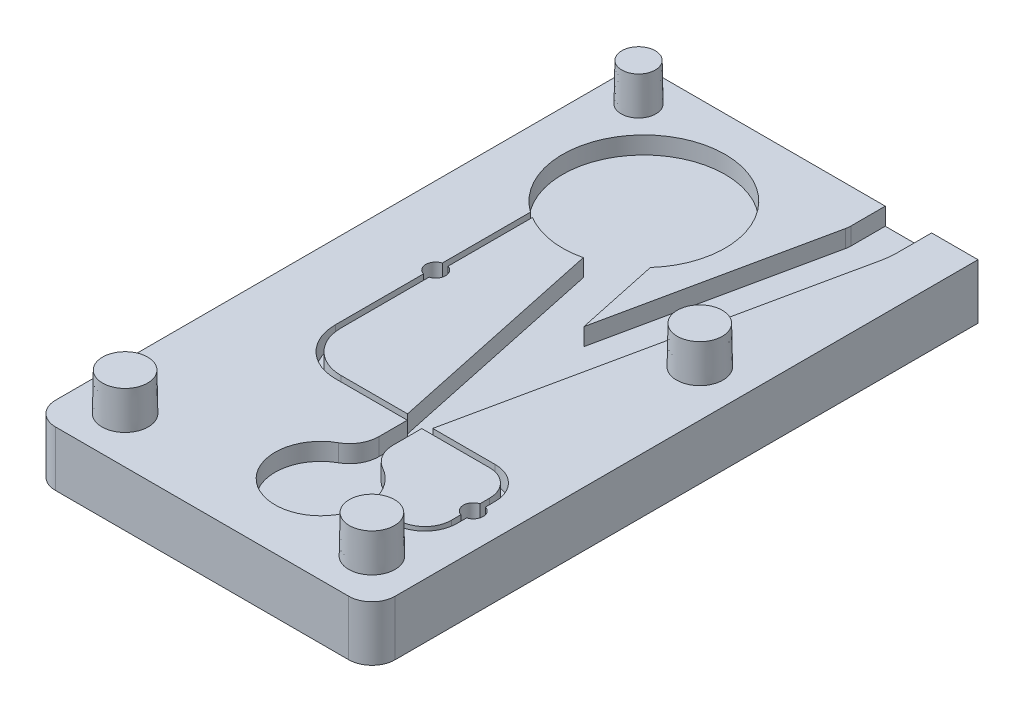
SolidWorks part; units mm, degrees
material "ABS"
ref_plane "Front Plane" through (0, 0, 0) normal (0, 0, 1) x (1, 0, 0)
ref_plane "Top Plane" through (0, 0, 0) normal (0, 1, 0) x (1, 0, 0)
ref_plane "Right Plane" through (0, 0, 0) normal (1, 0, 0) x (0, 0, -1)
sketch "Sketch1" plane through (0, 0, 0) normal (0, 1, 0) x (1, 0, 0)
  line L1 (-23.25, 41.5) -> (23.25, 41.5)
  line L2 (-23.25, 41.5) -> (-23.25, -41.5)
  line L3 (-23.25, -41.5) -> (23.25, -41.5)
  line L4 (23.25, 41.5) -> (23.25, -41.5)
  line L5 (-23.25, 41.5) -> (23.25, -41.5) construction
  line L6 (-23.25, -41.5) -> (23.25, 41.5) construction
  point P0 (0, 0)
  dimension "D1" = 46.5
  dimension "D2" = 83
extrude "Boss-Extrude1" add sketch "Sketch1" along normal blind 7.5406
sketch "Sketch2" plane through (0, 0, 0) normal (0, 1, 0) x (1, 0, 0)
  line L1 (-12.65, -10.23) -> (-12.65, 25.55) construction
  line L11 (9.4726, 31.3805) -> (10.4806, 36.123)
  line L17 (10.55, 36.7831) -> (10.55, 41.5)
  line L22 (-23.25, -41.5) -> (23.25, -41.5) construction
  line L23 (0.7075, -41.5) -> (7.6925, -41.5)
  line L24 (0.7075, -41.5) -> (0.7075, -34.6481)
  line L25 (9.4726, 31.3805) -> (4.2, 6.575)
  line L26 (15.6838, 30.0603) -> (16.6919, 34.8027)
  line L27 (4.2, 6.575) -> (0.1667, 25.55)
  line L28 (16.9, 36.7831) -> (16.9, 41.5)
  line L29 (0.1667, 25.55) -> (-6.0445, 24.2298)
  line L30 (-6.0445, 24.2298) -> (2.4737, -15.845)
  line L31 (-6.65, -16.23) -> (14.4748, -16.23) construction
  line L32 (3.2078, -16.615) -> (3.2078, -23.2943)
  line L33 (5.1922, -23.2943) -> (5.1922, -16.615)
  line L34 (4.2, 6.575) -> (4.2, 41.5) construction
  line L35 (18.4748, -20.23) -> (18.4748, -25.465) construction
  line L36 (14.4748, -29.465) -> (4.2, -29.465) construction
  line L37 (0.7075, -34.6481) -> (7.6925, -34.6481)
  line L38 (7.6925, -41.5) -> (7.6925, -34.6481)
  line L39 (15.6838, 30.0603) -> (5.9263, -15.845)
  line L40 (23.25, 41.5) -> (-23.25, 41.5) construction
  line L41 (4.2, 6.575) -> (10.6919, 6.575) construction
  line L42 (23.25, -41.5) -> (23.25, 41.5) construction
  line L43 (-23.25, 41.5) -> (-23.25, -41.5) construction
  line L44 (14.4748, -29.85) -> (4.2, -29.85)
  line L45 (18.8598, -20.23) -> (18.8598, -25.465)
  line L46 (-6.65, -15.845) -> (14.4748, -15.845)
  line L47 (-12.265, -10.23) -> (-12.265, 25.55)
  line L48 (14.4748, -29.08) -> (4.2, -29.08)
  line L49 (18.0898, -20.23) -> (18.0898, -25.465)
  line L50 (-6.65, -16.615) -> (14.4748, -16.615)
  line L51 (-13.035, -10.23) -> (-13.035, 25.55)
  line L52 (9.4726, 31.3805) -> (15.6838, 30.0603) construction
  line L53 (3.2078, -19.9546) -> (5.1922, -19.9546) construction
  line L54 (4.2, -19.9546) -> (4.2, -29.465) construction
  line L55 (10.55, 41.5) -> (16.9, 41.5)
  circle A6 centre (-6.56, 25.55) radius 11.13
  arc A7 (14.4748, -16.23) -> (18.4748, -20.23) centre (14.4748, -20.23) cw construction
  arc A8 (18.4748, -25.465) -> (14.4748, -29.465) centre (14.4748, -25.465) cw construction
  circle A9 centre (4.2, -29.465) radius 6.25
  arc A11 (-12.65, -10.23) -> (-6.65, -16.23) centre (-6.65, -10.23) ccw construction
  arc A12 (18.8598, -25.465) -> (14.4748, -29.85) centre (14.4748, -25.465) cw
  arc A13 (14.4748, -15.845) -> (18.8598, -20.23) centre (14.4748, -20.23) cw
  arc A14 (-12.265, -10.23) -> (-6.65, -15.845) centre (-6.65, -10.23) ccw
  arc A15 (18.0898, -25.465) -> (14.4748, -29.08) centre (14.4748, -25.465) cw
  arc A16 (14.4748, -16.615) -> (18.0898, -20.23) centre (14.4748, -20.23) cw
  arc A17 (-13.035, -10.23) -> (-6.65, -16.615) centre (-6.65, -10.23) ccw
  arc A18 (5.1922, -20.5129) -> (7.244, -24.0064) centre (9.1922, -20.5129) ccw
  arc A19 (1.156, -24.0064) -> (3.2078, -20.5129) centre (-0.7922, -20.5129) ccw
  circle A20 centre (-6.56, 25.55) radius 7.95 construction
  circle A21 centre (-6.56, 25.55) radius 9.525 construction
  arc A22 (10.4806, 36.123) -> (10.55, 36.7831) centre (7.375, 36.7831) ccw
  arc A23 (16.6919, 34.8027) -> (16.9, 36.7831) centre (7.375, 36.7831) ccw
  point P80 (13.725, 41.5)
  dimension "D18" = 14.2748
  dimension "D19" = 3.4527
  dimension "D20" = 19.05
  dimension "D25" = 9.525
  dimension "D26" = 9.525
  dimension "D16" = 6.985
  dimension "D13" = 6
  dimension "D6" = 22.26
  dimension "D14" = 12.5
  dimension "D17" = 4
  dimension "D22" = 4
  dimension "D23" = 15.9
  dimension "D24" = 19.05
  dimension "D1" = 34.925
  dimension "D2" = 12.5581
  dimension "D3" = 12
  dimension "D4" = 1.9844
  dimension "D5" = 16.69
  dimension "D7" = 10.6
  dimension "D8" = 15.95
  dimension "D9" = 6.35
  dimension "D10" = 0.385
  dimension "D11" = 0.385
  dimension "D12" = 25.27
  dimension "D15" = 12.85
  dimension "D21" = 6.35
extrude "Cut-Extrude3" cut sketch "Sketch2" against normal blind 2.3813 from surface at 7.5406
hole_wizard "1/4 NPT Tapped Hole1" [suppressed] positions "Sketch4" profile "Sketch6" size "1/4" standard "ANSI Inch"
sketch "Sketch4" plane through (0, 0, 41.5) normal (0, 0, 1) x (1, 0, 0)
  line L2 (4.2, -3.9624) -> (4.2, 3.9688) construction
  line L3 (9.2, 3.9688) -> (-0.8, 3.9688) construction
  line L4 (9.2, 6.35) -> (23.25, 6.35) construction
  point P2 (4.2, -3.9624)
  dimension "D1" = 10.3124
sketch "Sketch6" plane through (4.2, -3.9624, 41.5) normal (1, 0, 0) x (0, -1, 0)
  line L0 (0, 0) -> (0, 17.6298)
  line L1 (5.5626, 14.2875) -> (0, 17.6298)
  line L2 (-5.5626, 14.2875) -> (0, 17.6298) construction
  line L3 (5.5626, 14.2875) -> (5.5626, 10.033)
  line L4 (5.5626, 10.033) -> (6.558, 10.033)
  line L5 (6.558, 10.033) -> (6.8584, 0)
  line L6 (-6.558, 10.033) -> (-6.8584, 0) construction
  line L7 (6.8584, 0) -> (0, 0)
  line L8 (0, -6.35) -> (0, 107.95) construction
  line L11 (-5.5626, 10.033) -> (-6.558, 10.033) construction
  dimension "Tap Drill Dia." = 11.1252
  dimension "Tap Drill Depth" = 14.2875
  dimension "Thread Dia." = 13.7168
  dimension "Thread Angle" = 3.43
  dimension "Thread Depth" = 10.033
  dimension "Drill Angle" = 118
sketch "Sketch7" plane through (0, 7.5406, 0) normal (0, 1, 0) x (1, 0, 0)
  circle A9 centre (4.2, -29.465) radius 6.25
  arc A10 (1.156, -24.0064) -> (10.4381, -29.85) centre (4.2, -29.465) ccw construction
extrude "Cut-Extrude4" [suppressed] cut sketch "Sketch7" against normal blind 10.3124
sketch "Sketch8" plane through (0, 5.1594, 0) normal (0, 1, 0) x (1, 0, 0)
  circle A3 centre (-6.56, 25.55) radius 11.13
  arc A5 (1.7424, 18.1373) -> (-13.035, 16.4973) centre (-6.56, 25.55) ccw construction
extrude "Cut-Extrude5" [suppressed] cut sketch "Sketch8" against normal through all
sketch "Sketch10" plane through (0, 7.5406, 0) normal (0, 1, 0) x (1, 0, 0)
  line L0 (-13.035, 3.1337) -> (-12.265, 3.1337) construction
  line L1 (-13.035, 16.4973) -> (-13.035, -10.23) construction
  line L2 (-12.265, 15.9933) -> (-12.265, -10.23) construction
  line L3 (18.0898, -22.8475) -> (18.8598, -22.8475) construction
  line L4 (18.0898, -25.465) -> (18.0898, -20.23) construction
  line L5 (18.8598, -25.465) -> (18.8598, -20.23) construction
  circle A0 centre (18.4748, -22.8475) radius 1.3525
  circle A1 centre (-12.65, 3.1337) radius 1.3526
  dimension "D1" = 2.7051
  dimension "D2" = 2.7051
extrude "Cut-Extrude6" cut sketch "Sketch10" against normal offset from surface (4.7689 mm away) 2.3876 up to face at (11.8583, 5.1594, 22.6844)
sketch "Sketch11" plane through (0, 7.5406, 0) normal (0, 1, 0) x (1, 0, 0)
  line L0 (10.55, 41.5) -> (-23.25, 41.5) construction
  line L1 (-10.0525, 41.5) -> (-3.0675, 41.5)
  line L2 (-10.0525, 41.5) -> (-10.0525, 36.1178)
  line L3 (-10.0525, 36.1178) -> (-3.0675, 36.1178)
  line L4 (-3.0675, 41.5) -> (-3.0675, 36.1178)
  arc A0 (1.7424, 18.1373) -> (-13.035, 16.4973) centre (-6.56, 25.55) ccw construction
  arc A1 (1.7424, 18.1373) -> (-13.035, 16.4973) centre (-6.56, 25.55) ccw construction
  dimension "D1" = 6.985
extrude "Cut-Extrude7" [suppressed] cut sketch "Sketch11" against normal up to surface (2.3813 mm away)
sketch "Sketch12" plane through (0, 7.5406, 0) normal (0, 1, 0) x (1, 0, 0)
  line L0 (-23.25, 41.5) -> (-23.25, -41.5) construction
  line L1 (10.55, 41.5) -> (-23.25, 41.5) construction
  line L2 (-23.25, -41.5) -> (23.25, -41.5) construction
  line L3 (-23.25, -41.5) -> (23.25, -41.5) construction
  line L4 (23.25, -41.5) -> (23.25, 41.5) construction
  line L5 (23.25, 41.5) -> (16.9, 41.5) construction
  circle A0 centre (-16.9, -35.15) radius 3.175
  circle A1 centre (16.9, -35.15) radius 3.175
  circle A2 centre (16.9, 9.75) radius 3.175
  circle A3 centre (-18.4748, 36.7375) radius 2.3813
  dimension "D1" = 4.7625
  dimension "D2" = 6.35
  dimension "D3" = 6.35
  dimension "D4" = 6.35
  dimension "D5" = 4.7752
  dimension "D6" = 4.7625
  dimension "D7" = 6.35
  dimension "D8" = 6.35
  dimension "D9" = 6.35
  dimension "D10" = 6.35
  dimension "D11" = 6.35
  dimension "D12" = 31.75
extrude "Boss-Extrude2" add sketch "Sketch12" along normal blind 5.1594 draft 1
fillet "Fillet1" radius 3.175 3 edges at (-23.25, 3.7703, -41.5) (-23.25, 3.7703, 41.5) (23.25, 3.7703, 41.5)
